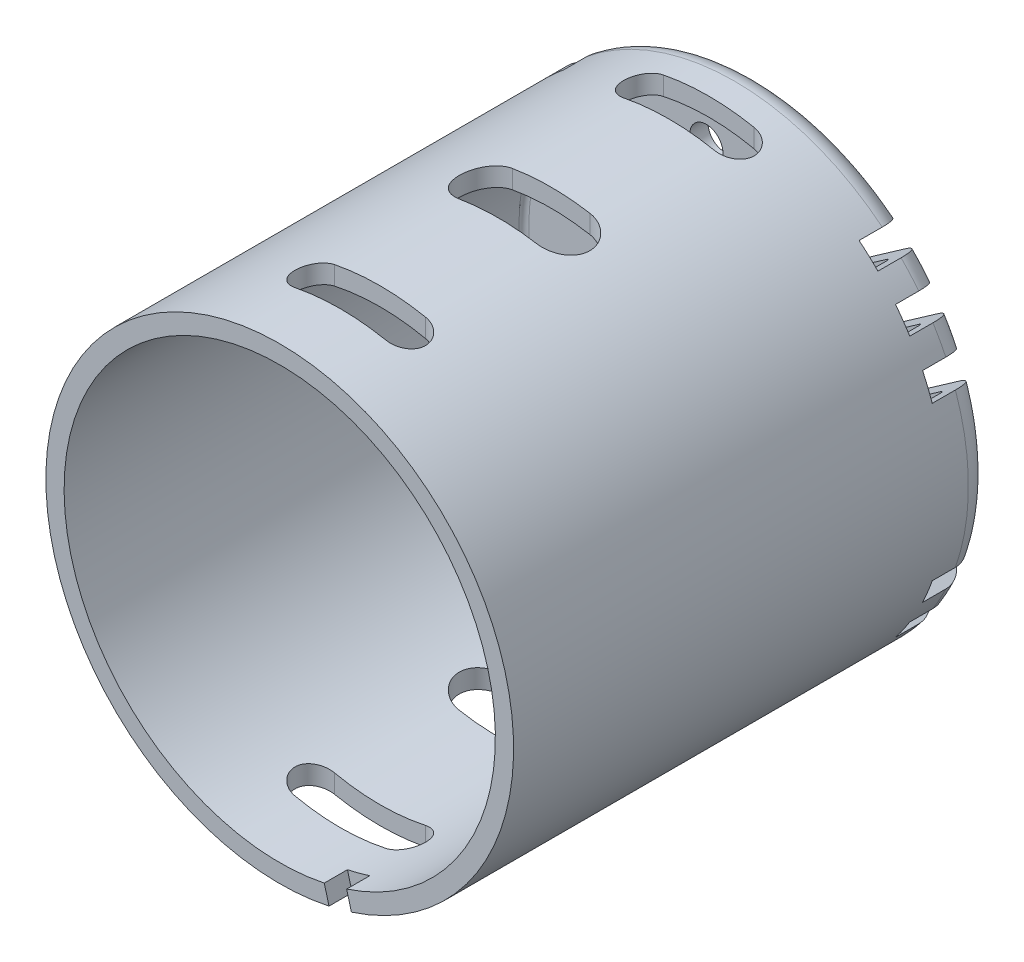
SolidWorks part; units mm, degrees
ref_plane "Front Plane" through (0, 0, 0) normal (0, 0, 1) x (1, 0, 0)
ref_plane "Top Plane" through (0, 0, 0) normal (0, 1, 0) x (1, 0, 0)
ref_plane "Right Plane" through (0, 0, 0) normal (1, 0, 0) x (0, 0, -1)
sketch "Sketch1" plane through (0, 0, 0) normal (1, 0, 0) x (0, 0, -1)
  line L0 (0, 0) -> (-40.2844, 0) construction
  line L1 (0, 2.8448) -> (0, 4.6101)
  line L2 (-1.016, 5.6261) -> (-3.5052, 5.6261)
  line L3 (-3.6322, 6.8453) -> (-3.6322, 16.1544)
  line L4 (-5.4102, 17.9324) -> (-40.2844, 17.9324)
  line L5 (-40.2844, 17.9324) -> (-40.2844, 0)
  line L6 (0, 2.8448) -> (-3.4389, 2.8448)
  line L7 (-3.4389, 2.8448) -> (-3.4389, 0)
  line L8 (-40.2844, 0) -> (-3.4389, 0)
  line L10 (-4.0132, 6.1341) -> (-4.0132, 6.5151)
  line L11 (-3.8862, 6.6421) -> (-3.8354, 6.6421)
  arc A0 (-3.6322, 16.1544) -> (-5.4102, 17.9324) centre (-5.4102, 16.1544) ccw
  arc A1 (0, 4.6101) -> (-1.016, 5.6261) centre (-1.016, 4.6101) ccw
  arc A2 (-3.5052, 5.6261) -> (-4.0132, 6.1341) centre (-3.5052, 6.1341) cw
  arc A3 (-3.8862, 6.6421) -> (-4.0132, 6.5151) centre (-3.8862, 6.5151) ccw
  arc A4 (-3.6322, 6.8453) -> (-3.8354, 6.6421) centre (-3.8354, 6.8453) cw
  point P9 (-3.6322, 17.9324)
  point P12 (0, 5.6261)
  dimension "D4" = 36.6522
revolve "Revolve1" add sketch "Sketch1" angle 360 about L0
sketch "Sketch2" plane through (0, 0, 0) normal (0, 0, -1) x (-1, 0, 0)
  circle A0 centre (0, 0) radius 2.8448 construction
  circle A1 centre (0, 0) radius 2.8448
extrude "Cut-Extrude1" cut sketch "Sketch2" against normal through all
shell "Shell1" thickness 1.397
sketch "Sketch3" plane through (0, 0, 40.2844) normal (0, 0, 1) x (1, 0, 0)
  circle A0 centre (0, 0) radius 4.2418 construction
  circle A1 centre (0, 0) radius 4.2418
extrude "Cut-Extrude2" cut sketch "Sketch3" against normal blind 39.37
sketch "Sketch5" plane through (0, 0, 0.9144) normal (0, 0, 1) x (1, 0, 0)
  circle A0 centre (0, 0) radius 4.7498
  dimension "D2" = 9.4996
extrude "Cut-Extrude7" cut sketch "Sketch5" along normal blind 25.4
sketch "Sketch6" plane through (0, 0, 3.6322) normal (0, 0, -1) x (-1, 0, 0)
  line L0 (0, 0) -> (-30.3518, 0) construction
  line L1 (0, 0) -> (0, 18.9368) construction
  line L2 (0, 0) -> (-25.5762, 17.9087) construction
  line L3 (-16.4656, 11.5294) -> (-8.4682, 5.9295) construction
  line L4 (-15.9193, 12.3096) -> (-7.9219, 6.7098)
  line L5 (-17.012, 10.7491) -> (-9.0146, 5.1493)
  line L6 (-16.4656, -11.5294) -> (-8.4682, -5.9295) construction
  line L7 (-15.9193, -12.3096) -> (-7.9219, -6.7098)
  line L8 (-17.012, -10.7491) -> (-9.0146, -5.1493)
  line L9 (16.4656, 11.5294) -> (8.4682, 5.9295) construction
  line L10 (15.9193, 12.3096) -> (7.9219, 6.7098)
  line L11 (17.012, 10.7491) -> (9.0146, 5.1493)
  line L12 (2.2582, 3.225) -> (-23.318, 21.1337)
  line L13 (-2.2582, -3.225) -> (-27.8344, 14.6837)
  line L14 (-14.314, 14.829) -> (-5.5719, 8.7077) construction
  line L15 (-13.7677, 15.6092) -> (-5.0256, 9.4879)
  line L16 (-14.8604, 14.0487) -> (-6.1182, 7.9274)
  line L17 (-19.3309, 8.7294) -> (-10.0883, 2.2577) construction
  line L18 (-18.7845, 9.5097) -> (-9.5419, 3.0379)
  line L19 (-19.8772, 7.9492) -> (-10.6346, 1.4774)
  line L20 (-19.3309, -8.7294) -> (-10.0883, -2.2577) construction
  line L21 (-18.7845, -9.5097) -> (-9.5419, -3.0379)
  line L22 (-19.8772, -7.9492) -> (-10.6346, -1.4774)
  line L23 (-14.314, -14.829) -> (-5.5719, -8.7077) construction
  line L24 (-13.7677, -15.6092) -> (-5.0256, -9.4879)
  line L25 (-14.8604, -14.0487) -> (-6.1182, -7.9274)
  line L26 (19.3309, 8.7294) -> (10.0883, 2.2577) construction
  line L27 (18.7845, 9.5097) -> (9.5419, 3.0379)
  line L28 (19.8772, 7.9492) -> (10.6346, 1.4774)
  line L29 (14.314, 14.829) -> (5.5719, 8.7077) construction
  line L30 (13.7677, 15.6092) -> (5.0256, 9.4879)
  line L31 (14.8604, 14.0487) -> (6.1182, 7.9274)
  line L32 (14.314, -14.829) -> (5.5719, -8.7077) construction
  line L33 (13.7677, -15.6092) -> (5.0256, -9.4879)
  line L34 (14.8604, -14.0487) -> (6.1182, -7.9274)
  line L35 (16.4656, -11.5294) -> (8.4682, -5.9295) construction
  line L36 (15.9193, -12.3096) -> (7.9219, -6.7098)
  line L37 (17.012, -10.7491) -> (9.0146, -5.1493)
  line L38 (19.3309, -8.7294) -> (10.0883, -2.2577) construction
  line L39 (18.7845, -9.5097) -> (9.5419, -3.0379)
  line L40 (19.8772, -7.9492) -> (10.6346, -1.4774)
  circle A0 centre (0, 0) radius 6.8453 construction
  circle A1 centre (0, 0) radius 6.8453
  circle A2 centre (0, 0) radius 9.3853
  arc A3 (-15.9193, 12.3096) -> (-17.012, 10.7491) centre (-16.4656, 11.5294) ccw
  arc A4 (-9.0146, 5.1493) -> (-7.9219, 6.7098) centre (-8.4682, 5.9295) ccw
  arc A5 (-15.9193, -12.3096) -> (-17.012, -10.7491) centre (-16.4656, -11.5294) cw
  arc A6 (-9.0146, -5.1493) -> (-7.9219, -6.7098) centre (-8.4682, -5.9295) cw
  arc A7 (15.9193, 12.3096) -> (17.012, 10.7491) centre (16.4656, 11.5294) cw
  arc A8 (9.0146, 5.1493) -> (7.9219, 6.7098) centre (8.4682, 5.9295) cw
  arc A9 (-13.7677, 15.6092) -> (-14.8604, 14.0487) centre (-14.314, 14.829) ccw
  arc A10 (-6.1182, 7.9274) -> (-5.0256, 9.4879) centre (-5.5719, 8.7077) ccw
  arc A11 (-18.7845, 9.5097) -> (-19.8772, 7.9492) centre (-19.3309, 8.7294) ccw
  arc A12 (-10.6346, 1.4774) -> (-9.5419, 3.0379) centre (-10.0883, 2.2577) ccw
  arc A13 (-18.7845, -9.5097) -> (-19.8772, -7.9492) centre (-19.3309, -8.7294) cw
  arc A14 (-10.6346, -1.4774) -> (-9.5419, -3.0379) centre (-10.0883, -2.2577) cw
  arc A15 (-13.7677, -15.6092) -> (-14.8604, -14.0487) centre (-14.314, -14.829) cw
  arc A16 (-6.1182, -7.9274) -> (-5.0256, -9.4879) centre (-5.5719, -8.7077) cw
  arc A17 (18.7845, 9.5097) -> (19.8772, 7.9492) centre (19.3309, 8.7294) cw
  arc A18 (10.6346, 1.4774) -> (9.5419, 3.0379) centre (10.0883, 2.2577) cw
  arc A19 (13.7677, 15.6092) -> (14.8604, 14.0487) centre (14.314, 14.829) cw
  arc A20 (6.1182, 7.9274) -> (5.0256, 9.4879) centre (5.5719, 8.7077) cw
  arc A21 (13.7677, -15.6092) -> (14.8604, -14.0487) centre (14.314, -14.829) ccw
  arc A22 (6.1182, -7.9274) -> (5.0256, -9.4879) centre (5.5719, -8.7077) ccw
  arc A23 (15.9193, -12.3096) -> (17.012, -10.7491) centre (16.4656, -11.5294) ccw
  arc A24 (9.0146, -5.1493) -> (7.9219, -6.7098) centre (8.4682, -5.9295) ccw
  arc A25 (18.7845, -9.5097) -> (19.8772, -7.9492) centre (19.3309, -8.7294) ccw
  arc A26 (10.6346, -1.4774) -> (9.5419, -3.0379) centre (10.0883, -2.2577) ccw
  point P13 (-12.4669, 8.7294)
  point P20 (-12.4669, -8.7294)
  point P27 (12.4669, 8.7294)
  point P38 (-9.943, 11.7683)
  point P45 (-14.7096, 5.4936)
  point P52 (-14.7096, -5.4936)
  point P59 (-9.943, -11.7683)
  point P66 (14.7096, 5.4936)
  point P73 (9.943, 11.7683)
  point P80 (9.943, -11.7683)
  point P87 (12.4669, -8.7294)
  point P94 (14.7096, -5.4936)
  dimension "D1" = 35
  dimension "D3" = 1.905
  dimension "D6" = 1.905
  dimension "D7" = 1.905
  dimension "D2" = 2.54
  dimension "D4" = 3.937
  dimension "D5" = 3.937
extrude "Cut-Extrude8" cut sketch "Sketch6" against normal blind 3.556 contours L15 A10 L16 A9 | L4 A4 L5 A3 | L18 A12 L19 A11 | L30 A20 L31 A19 | L10 A8 L11 A7 | L27 A18 L28 A17 | L40 A26 L39 A25 | L37 A24 L36 A23 | L34 A22 L33 A21 | L25 A16 L24 A15 | L8 A6 L7 A5 | L22 A14 L21 A13
sketch "Sketch7" plane through (0, 0, 3.6322) normal (0, 0, -1) x (-1, 0, 0)
  line L0 (0, 1.1811) -> (0, 20.4063) construction
  line L1 (0, 0) -> (-25.8819, 0) construction
  circle A0 centre (-2.54, 12.3317) radius 1.27
  circle A1 centre (2.54, 12.3317) radius 1.27
  circle A2 centre (2.54, -12.3317) radius 1.27
  circle A3 centre (-2.54, -12.3317) radius 1.27
  dimension "D1" = 2.54
  dimension "D2" = 2.54
  dimension "D3" = 12.3317
extrude "Cut-Extrude9" cut sketch "Sketch7" against normal through all
sketch "Sketch8" plane through (0, 0, 0) normal (0, 1, 0) x (1, 0, 0)
  line L0 (2.8448, 0) -> (-2.8448, 0) construction
  line L1 (-17.9324, -5.4102) -> (-17.9324, -40.2844) construction
  line L2 (2.8448, 0) -> (-2.8448, 0)
  line L3 (-17.9324, -5.4102) -> (-17.9324, -40.2844)
  line L4 (-17.9324, -40.2844) -> (17.9324, -40.2844) construction
  line L5 (-17.9324, -40.2844) -> (17.9324, -40.2844)
  line L6 (0, -40.2844) -> (0, 2.2619) construction
  line L7 (0, -34.1122) -> (-22.5931, -34.1122) construction
  line L8 (0, -8.9154) -> (-22.5931, -8.9154)
  line L9 (0, -21.5138) -> (-22.5931, -21.5138)
  line L10 (-3.4798, -34.1122) -> (3.4798, -34.1122) construction
  line L11 (-3.4798, -32.5882) -> (3.4798, -32.5882)
  line L12 (-3.4798, -35.6362) -> (3.4798, -35.6362)
  line L13 (-3.4798, -8.9154) -> (3.4798, -8.9154) construction
  line L14 (-3.4798, -10.4394) -> (3.4798, -10.4394)
  line L15 (-3.4798, -7.3914) -> (3.4798, -7.3914)
  line L16 (-2.9718, -21.5138) -> (2.9718, -21.5138) construction
  line L17 (-2.9718, -19.4818) -> (2.9718, -19.4818)
  line L18 (-2.9718, -23.5458) -> (2.9718, -23.5458)
  arc A0 (-3.4798, -32.5882) -> (-3.4798, -35.6362) centre (-3.4798, -34.1122) ccw
  arc A1 (3.4798, -35.6362) -> (3.4798, -32.5882) centre (3.4798, -34.1122) ccw
  arc A2 (-3.4798, -10.4394) -> (-3.4798, -7.3914) centre (-3.4798, -8.9154) cw
  arc A3 (3.4798, -7.3914) -> (3.4798, -10.4394) centre (3.4798, -8.9154) cw
  arc A4 (-2.9718, -19.4818) -> (-2.9718, -23.5458) centre (-2.9718, -21.5138) ccw
  arc A5 (2.9718, -23.5458) -> (2.9718, -19.4818) centre (2.9718, -21.5138) ccw
  point P16 (0, -34.1122)
  point P23 (0, -8.9154)
  point P30 (0, -21.5138)
  dimension "D5" = 6.9596
  dimension "D1" = 6.1722
  dimension "D4" = 3.048
  dimension "D6" = 4.064
  dimension "D7" = 5.9436
  dimension "D2" = 25.1968
  dimension "D3" = 12.5984
extrude "Cut-Extrude10" cut sketch "Sketch8" against normal through all and the other way through all contours L14 A3 L15 A2 | L18 A5 L17 A4 | L11 A1 L12 A0
sketch "Sketch10" plane through (0, 0, 40.2844) normal (0, 0, 1) x (1, 0, 0)
  line L0 (3.4148, -16.179) -> (3.7768, -17.5302)
  line L1 (0, 0) -> (0, -19.8721) construction
  line L2 (5.1322, -15.7188) -> (5.4942, -17.07)
  line L3 (0, 0) -> (4.6412, -17.3214) construction
  circle A0 centre (0, 0) radius 17.9324 construction
  circle A1 centre (0, 0) radius 16.5354 construction
  arc A2 (3.7768, -17.5302) -> (5.4942, -17.07) centre (0, 0) ccw
  arc A3 (3.4148, -16.179) -> (5.1322, -15.7188) centre (0, 0) ccw
  point P1 (-0.7699, -0.4445)
  point P3 (9.3415, -17.958)
  point P4 (10.1114, -17.5135)
  point P5 (0.7699, 0.4445)
  point P6 (10.8813, -17.069)
  dimension "D1" = 0.889
  dimension "D3" = 15
extrude "Cut-Extrude11" cut sketch "Sketch10" against normal blind 1.778
